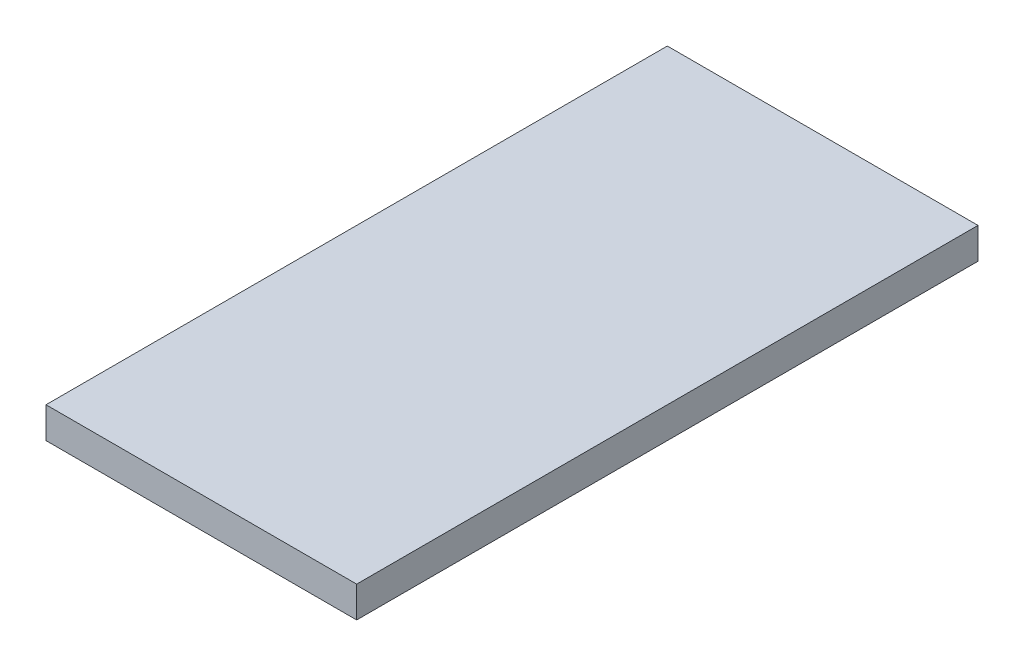
SolidWorks part; units mm, degrees
ref_plane "Front Plane" through (0, 0, 0) normal (0, 0, 1) x (1, 0, 0)
ref_plane "Top Plane" through (0, 0, 0) normal (0, 1, 0) x (1, 0, 0)
ref_plane "Right Plane" through (0, 0, 0) normal (1, 0, 0) x (0, 0, -1)
sketch "Sketch1" plane through (0, 0, 0) normal (0, 1, 0) x (1, 0, 0)
  line L1 (-31.75, -63.5) -> (31.75, -63.5)
  line L2 (-31.75, -63.5) -> (-31.75, 63.5)
  line L3 (-31.75, 63.5) -> (31.75, 63.5)
  line L4 (31.75, -63.5) -> (31.75, 63.5)
  line L5 (-31.75, -63.5) -> (31.75, 63.5) construction
  line L6 (-31.75, 63.5) -> (31.75, -63.5) construction
  point P0 (0, 0)
  dimension "D1" = 63.5
  dimension "D2" = 127
extrude "Boss-Extrude1" add sketch "Sketch1" along normal mid plane 6.35
hole_wizard "#2-56 Tapped Hole1" positions "Sketch3" profile "Sketch2" tap size "#2-56" standard "Ansi Inch"
sketch "Sketch3" plane through (-31.75, 0, 0) normal (-1, 0, 0) x (0, 0, 1)
  point P0 (-22.225, 0)
sketch "Sketch2" plane through (-31.75, 0, -22.225) normal (0, 1, 0) x (0, 0, 1)
  line L0 (0, 0) -> (0, 6.1222)
  line L1 (0, 6.1222) -> (0.889, 5.588)
  line L2 (0.889, 5.588) -> (0.889, 0)
  line L5 (0.889, 0) -> (0, 0)
  line L10 (0, 6.1222) -> (-0.889, 5.588) construction
  line L11 (0, -6.35) -> (0, 107.95) construction
  dimension "Tap Drill Dia." = 1.778
  dimension "Tap Drill Depth" = 5.588
  dimension "Drill Angle" = 118
cosmetic thread "Hole Thread1" parameters "D1"=4.318, "D2"=2.1844
